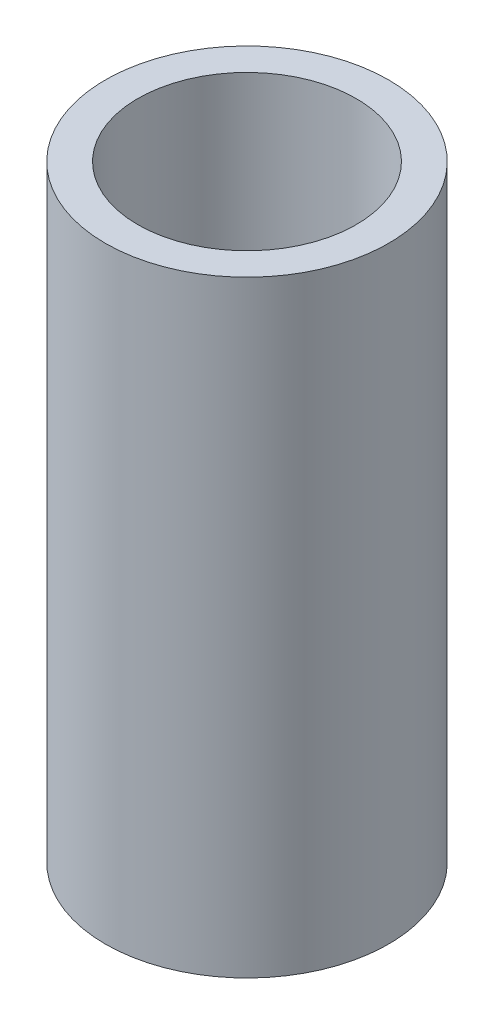
SolidWorks part; units mm, degrees
ref_plane "Front Plane" through (0, 0, 0) normal (0, 0, 1) x (1, 0, 0)
ref_plane "Top Plane" through (0, 0, 0) normal (0, 1, 0) x (1, 0, 0)
ref_plane "Right Plane" through (0, 0, 0) normal (1, 0, 0) x (0, 0, -1)
sketch "Sketch2" plane through (0, 0, 0) normal (0, 1, 0) x (1, 0, 0)
  circle A0 centre (0, 0) radius 3.5
  circle A1 centre (0, 0) radius 2.7
  dimension "D1" = 5.4
  dimension "D2" = 7
extrude "Boss-Extrude1" add sketch "Sketch2" along normal blind 15
